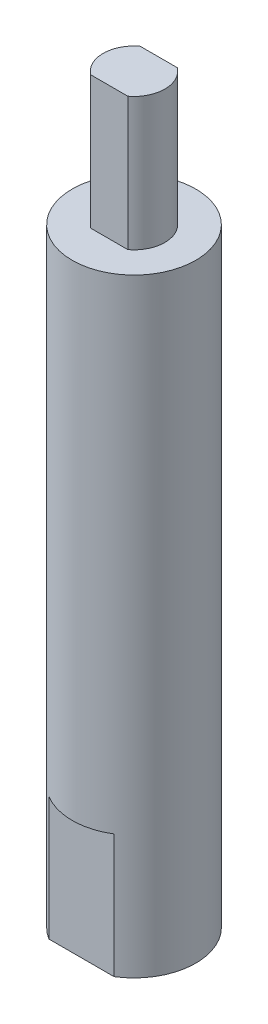
SolidWorks part; units mm, degrees
material "ACIER"
ref_plane "Plan de face" through (0, 0, 0) normal (0, 0, 1) x (1, 0, 0)
ref_plane "Plan de dessus" through (0, 0, 0) normal (0, 1, 0) x (1, 0, 0)
ref_plane "Plan de droite" through (0, 0, 0) normal (1, 0, 0) x (0, 0, -1)
sketch "Esquisse1" plane through (0, 0, 0) normal (0, 1, 0) x (1, 0, 0)
  circle A0 centre (0, 0) radius 10
  dimension "D1" = 20
extrude "Boss.-Extru.1" add sketch "Esquisse1" along normal blind 120
sketch "Esquisse2" plane through (0, 120, 0) normal (0, 1, 0) x (1, 0, 0)
  circle A0 centre (0, 0) radius 5
  circle A1 centre (0, 0) radius 10 construction
  circle A2 centre (0, 0) radius 10
  dimension "D1" = 10
extrude "Enlèv. mat.-Extru.1" cut sketch "Esquisse2" against normal blind 21.5
hole_wizard "Trou taraudé M101" positions "Esquisse11" profile "Esquisse13" tap size "M10" standard "ISO"
sketch "Esquisse11" plane through (0, 0, 0) normal (0, -1, 0) x (-1, 0, 0)
  point P0 (0, 0)
sketch "Esquisse13" plane through (0, 0, 0) normal (1, 0, 0) x (0, 0, -1)
  line L0 (0, 0) -> (0, 37.5537)
  line L1 (0, 37.5537) -> (4.25, 35)
  line L2 (4.25, 35) -> (4.25, 0.775)
  line L3 (4.25, 0.775) -> (5.025, 0)
  line L5 (5.025, 0) -> (0, 0)
  line L6 (-4.25, 0.775) -> (-5.025, 0) construction
  line L10 (0, 37.5537) -> (-4.25, 35) construction
  line L11 (0, -6.35) -> (0, 107.95) construction
  dimension "Diamètre du trou pour taraudage" = 8.5
  dimension "Profondeur du trou pour taraudage" = 35
  dimension "Diamètre du fraisage entrant" = 10.05
  dimension "Angle du fraisage entrant" = 90
  dimension "Angle de pointe" = 118
cosmetic thread "Filetage de perçage1" parameters "D1"=27.5, "D2"=10
sketch "Esquisse14" plane through (0, 0, 0) normal (0, -1, 0) x (1, 0, 0)
  line L0 (0, 0) -> (0, 9.25) construction
  line L1 (-10, 8.5) -> (10, 8.5)
  line L2 (-10, 8.5) -> (-10, 10)
  line L3 (-10, 10) -> (10, 10)
  line L4 (10, 8.5) -> (10, 10)
  line L5 (-10, 8.5) -> (10, 10) construction
  line L6 (-10, 10) -> (10, 8.5) construction
  line L7 (-10, -10) -> (10, -10)
  line L8 (-10, -10) -> (-10, -8.5)
  line L9 (-10, -8.5) -> (10, -8.5)
  line L10 (10, -10) -> (10, -8.5)
  line L11 (-10, -10) -> (10, -8.5) construction
  line L12 (-10, -8.5) -> (10, -10) construction
  line L13 (0, 0) -> (0, -9.25) construction
  line L14 (-11.6443, 0) -> (18.6009, 0) construction
  circle A0 centre (0, 0) radius 10 construction
  point P0 (0, 9.25)
  point P7 (0, -9.25)
  dimension "D1" = 17
  dimension "D2" = 20
  dimension "D3" = 20
extrude "Enlèv. mat.-Extru.2" cut sketch "Esquisse14" against normal blind 20
sketch "Esquisse15" plane through (0, 120, 0) normal (0, 1, 0) x (1, 0, 0)
  line L0 (-4.1929, 0) -> (3.9769, 0) construction
  line L1 (-10, 4) -> (10, 4)
  line L2 (-10, 4) -> (-10, 5)
  line L3 (-10, 5) -> (10, 5)
  line L4 (10, 4) -> (10, 5)
  line L5 (-10, 4) -> (10, 5) construction
  line L6 (-10, 5) -> (10, 4) construction
  line L7 (-10, -4) -> (10, -4)
  line L8 (-10, -4) -> (-10, -5)
  line L9 (-10, -5) -> (10, -5)
  line L10 (10, -4) -> (10, -5)
  line L11 (-10, -4) -> (10, -5) construction
  line L12 (-10, -5) -> (10, -4) construction
  line L13 (0, 2.6096) -> (0, -2.0867) construction
  circle A0 centre (0, 0) radius 5 construction
  point P0 (0, 4.5)
  point P5 (0, -4.5)
  dimension "D1" = 8
  dimension "D2" = 20
  dimension "D3" = 20
extrude "Enlèv. mat.-Extru.5" cut sketch "Esquisse15" against normal up to surface (21.5 mm away) up to face at (0, 98.5, 5)
